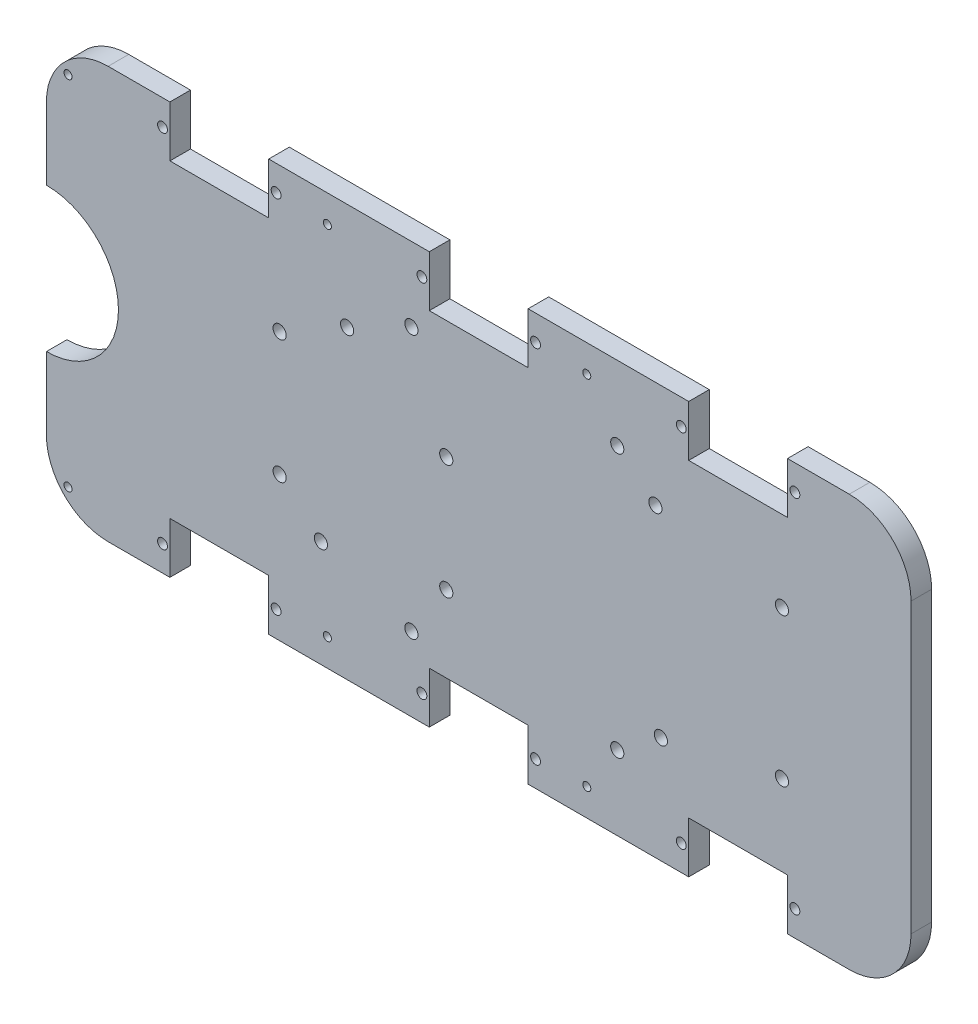
SolidWorks part; units mm, degrees
ref_plane "Front Plane" through (0, 0, 0) normal (0, 0, 1) x (1, 0, 0)
ref_plane "Top Plane" through (0, 0, 0) normal (0, 1, 0) x (1, 0, 0)
ref_plane "Right Plane" through (0, 0, 0) normal (1, 0, 0) x (0, 0, -1)
sketch "Sketch1" plane through (0, 0, 0) normal (0, 0, 1) x (1, 0, 0)
  line L1 (-90, -50) -> (90, -50)
  line L2 (-105, -35) -> (-105, 35)
  line L3 (-90, 50) -> (90, 50)
  line L4 (105, -35) -> (105, 35)
  line L5 (-105, -50) -> (105, 50) construction
  line L6 (-105, 50) -> (105, -50) construction
  arc A0 (-105, -35) -> (-90, -50) centre (-90, -35) ccw
  arc A1 (90, -50) -> (105, -35) centre (90, -35) ccw
  arc A2 (105, 35) -> (90, 50) centre (90, 35) ccw
  arc A3 (-90, 50) -> (-105, 35) centre (-90, 35) ccw
  point P0 (0, 0)
  dimension "D3" = 15
  dimension "D1" = 210
  dimension "D2" = 100
extrude "Boss-Extrude2" add sketch "Sketch1" along normal blind 5
sketch "Sketch2" plane through (0, 0, 5) normal (0, 0, 1) x (1, 0, 0)
  line L0 (-105, 0) -> (-75, 0) construction
  line L1 (-105, 35) -> (-105, -35) construction
  line L2 (-75, 0) -> (-51, 0) construction
  line L3 (-51, 0) -> (-12, 0) construction
  line L4 (-12, 0) -> (12, 0) construction
  line L5 (12, 0) -> (51, 0) construction
  line L6 (51, 0) -> (75, 0) construction
  line L7 (-75, 0) -> (-75, 50) construction
  line L8 (90, 50) -> (-90, 50) construction
  line L9 (-51, 0) -> (-51, 50) construction
  line L10 (-12, 0) -> (-12, 50) construction
  line L11 (12, 0) -> (12, 50) construction
  line L12 (51, 0) -> (51, 50) construction
  line L13 (75, 0) -> (75, 50) construction
  line L14 (-75, 0) -> (-75, -50) construction
  line L15 (-90, -50) -> (90, -50) construction
  line L16 (-51, 0) -> (-51, -50) construction
  line L17 (-12, 0) -> (-12, -50) construction
  line L18 (12, 0) -> (12, -50) construction
  line L19 (51, 0) -> (51, -50) construction
  line L20 (75, 0) -> (75, -50) construction
  line L21 (51, -37.6) -> (75, -37.6)
  line L22 (-75, 50) -> (-51, 50)
  line L23 (-75, 50) -> (-75, 37.6)
  line L24 (-75, 37.6) -> (-51, 37.6)
  line L25 (-51, 50) -> (-51, 37.6)
  line L26 (-12, 50) -> (12, 50)
  line L27 (-12, 50) -> (-12, 37.6)
  line L28 (-12, 37.6) -> (12, 37.6)
  line L29 (12, 50) -> (12, 37.6)
  line L30 (51, 50) -> (75, 50)
  line L31 (51, 50) -> (51, 37.6)
  line L32 (51, 37.6) -> (75, 37.6)
  line L33 (75, 50) -> (75, 37.6)
  line L34 (75, -50) -> (75, -37.6)
  line L35 (51, -50) -> (75, -50)
  line L36 (51, -50) -> (51, -37.6)
  line L37 (-12, -37.6) -> (12, -37.6)
  line L38 (12, -50) -> (12, -37.6)
  line L39 (-12, -50) -> (12, -50)
  line L40 (-12, -50) -> (-12, -37.6)
  line L41 (-75, -37.6) -> (-51, -37.6)
  line L42 (-51, -50) -> (-51, -37.6)
  line L43 (-75, -50) -> (-51, -50)
  line L44 (-75, -50) -> (-75, -37.6)
  dimension "D1" = 30
  dimension "D2" = 24
  dimension "D3" = 39
  dimension "D4" = 24
  dimension "D5" = 39
  dimension "D6" = 24
  dimension "D7" = 12.4
  dimension "D8" = 12.4
extrude "Cut-Extrude1" cut sketch "Sketch2" against normal blind 5
sketch "Sketch3" plane through (0, 0, 5) normal (0, 0, 1) x (1, 0, 0)
  line L0 (-51, 50) -> (-51, 37.6) construction
  line L1 (-105, 0) -> (105, 0) construction
  line L2 (-75, 50) -> (-75, 37.6) construction
  line L3 (-105, 35) -> (-105, -35) construction
  line L4 (-75, 43.8) -> (-76.8, 43.8) construction
  line L5 (-51, 43.8) -> (-49.2, 43.8) construction
  line L6 (105, -35) -> (105, 35) construction
  circle A0 centre (-76.8, 43.8) radius 1.2
  circle A1 centre (-49.2, 43.8) radius 1.2
  circle A2 centre (-13.8, 43.8) radius 1.2
  circle A3 centre (13.8, 43.8) radius 1.2
  circle A4 centre (49.2, 43.8) radius 1.2
  circle A5 centre (76.8, 43.8) radius 1.2
  circle A6 centre (-76.8, -43.8) radius 1.2
  circle A7 centre (-49.2, -43.8) radius 1.2
  circle A8 centre (-13.8, -43.8) radius 1.2
  circle A9 centre (13.8, -43.8) radius 1.2
  circle A10 centre (49.2, -43.8) radius 1.2
  circle A11 centre (76.8, -43.8) radius 1.2
  dimension "D2" = 1.8
  dimension "D3" = 3
  dimension "D1" = 1.8
extrude "Cut-Extrude2" cut sketch "Sketch3" against normal blind 5
sketch "Sketch5" plane through (0, 0, 5) normal (0, 0, 1) x (1, 0, 0)
  line L0 (-51, 50) -> (-51, 37.6) construction
  line L1 (105, 0) -> (-95.1885, 0) construction
  line L2 (-12, 50) -> (-51, 50) construction
  line L3 (-51, 37.6) -> (-51, 50) construction
  line L4 (-31.5, 50) -> (-36.75, 50) construction
  line L5 (-36.75, 50) -> (-36.75, 43.3602) construction
  circle A4 centre (-36.75, 43.3602) radius 0.975
  circle A5 centre (26.25, 43.3602) radius 0.975
  circle A6 centre (26.25, -43.3602) radius 0.975
  circle A7 centre (-36.75, -43.3602) radius 0.975
  circle A8 centre (-99.75, 43.3602) radius 0.975
  circle A9 centre (-99.75, -43.3602) radius 0.975
  point P13 (105, 0)
  dimension "D1" = 2
  dimension "D2" = 2
extrude "Cut-Extrude3" cut sketch "Sketch5" against normal blind 10
sketch "Sketch6" plane through (0, 0, 5) normal (0, 0, 1) x (1, 0, 0)
  line L0 (75, 37.6) -> (75, -37.6) construction
  line L1 (-105, 35) -> (-105, -35) construction
  circle A0 centre (-105, 0) radius 17.5
extrude "Cut-Extrude4" cut sketch "Sketch6" against normal blind 10
sketch "Sketch8" plane through (0, 0, 0) normal (0, 0, -1) x (-1, 0, 0)
  line L0 (-63, 37.6) -> (-63, 0) construction
  line L1 (-51, 37.6) -> (-75, 37.6) construction
  line L2 (-63, 0) -> (-8.65, 0) construction
  line L3 (-8.65, 0) -> (31.97, 0) construction
  line L4 (31.97, 0) -> (31.97, 24.11) construction
  line L5 (-8.65, 0) -> (-8.65, -24.11) construction
  line L6 (-8.65, 0) -> (-42.91, 0) construction
  line L7 (-8.65, -24.11) -> (38.33, -24.11) construction
  line L8 (-8.65, 0) -> (7.88, 0) construction
  line L9 (7.88, 0) -> (7.88, -19.03) construction
  line L10 (7.88, 0) -> (7.88, 8.88) construction
  line L11 (-42.91, 0) -> (-42.91, 24.11) construction
  line L12 (-8.65, -24.11) -> (-44.24, -24.11) construction
  line L13 (-8.65, 0) -> (48.35, 0) construction
  line L14 (48.35, 0) -> (48.35, 15) construction
  line L15 (-8.65, 0) -> (-73.65, 0) construction
  line L16 (-73.65, 0) -> (-73.65, 18) construction
  line L17 (-8.65, 0) -> (-8.65, 32) construction
  line L18 (-8.65, 32) -> (-33.65, 32) construction
  circle A0 centre (31.97, 24.11) radius 1.6
  circle A3 centre (38.33, -24.11) radius 1.6
  circle A4 centre (7.88, 8.88) radius 1.6
  circle A5 centre (7.88, -19.03) radius 1.6
  circle A6 centre (-42.91, 24.11) radius 1.6
  circle A8 centre (-44.24, -24.11) radius 1.6
  circle A9 centre (-73.65, 18) radius 1.6
  circle A10 centre (48.35, 15) radius 1.6
  circle A11 centre (-73.65, -18) radius 1.6
  circle A12 centre (48.35, -15) radius 1.6
  circle A13 centre (-33.65, 32) radius 1.6
  circle A14 centre (16.35, 32) radius 1.6
  circle A15 centre (-33.65, -32) radius 1.6
  circle A16 centre (16.35, -32) radius 1.6
  dimension "D4" = 46.98
  dimension "D5" = 16.53
  dimension "D8" = 34.26
  dimension "D9" = 24.11
  dimension "D11" = 57
  dimension "D15" = 32
  dimension "D1" = 54.35
  dimension "D2" = 40.62
  dimension "D3" = 24.11
  dimension "D6" = 19.03
  dimension "D7" = 8.88
  dimension "D10" = 35.59
  dimension "D12" = 15
  dimension "D13" = 65
  dimension "D14" = 18
  dimension "D16" = 25
extrude "Cut-Extrude5" cut sketch "Sketch8" against normal blind 10
sketch "Sketch10" plane through (0, 0, 0) normal (0, 0, -1) x (-1, 0, 0)
  line L0 (71.2901, 0) -> (71.2901, -11.5)
  line L2 (76.2901, 0) -> (76.2901, -16.5)
  line L3 (65.0901, 11.5) -> (65.0901, 0) construction
  line L13 (53.8901, -16.5) -> (76.2901, -16.5)
  line L14 (53.8901, 16.5) -> (53.8901, -16.5)
  line L15 (87.5, 0) -> (71.2901, 0) construction
  line L16 (58.8901, 11.5) -> (71.2901, 11.5)
  line L17 (58.8901, 11.5) -> (58.8901, -11.5)
  line L18 (58.8901, -11.5) -> (71.2901, -11.5)
  line L20 (58.8901, 11.5) -> (71.2901, -11.5) construction
  line L21 (58.8901, -11.5) -> (71.2901, 11.5) construction
  line L24 (53.8901, 16.5) -> (71.2901, 16.5)
  line L25 (71.2901, 11.5) -> (71.2901, 16.5)
  line L26 (71.2901, 0) -> (76.2901, 0)
  line L27 (53.8901, 16.5) -> (76.2901, 16.5) construction
  line L28 (76.2901, 16.5) -> (76.2901, -16.5) construction
  line L29 (71.2901, 11.5) -> (71.2901, -11.5) construction
  arc A0 (105, 17.5) -> (105, -17.5) centre (105, 0) ccw construction
  dimension "D1" = 22.4099
  dimension "D2" = 23
  dimension "D3" = 12.4
  dimension "D4" = 5
extrude "Boss-Extrude3" add sketch "Sketch10" along normal blind 17.7
sketch "Sketch12" plane through (0, 0, -17.7) normal (0, 0, -1) x (-1, 0, 0)
  line L0 (58.8901, 0) -> (96.2, 0) construction
  line L1 (58.8901, 11.5) -> (58.8901, -11.5) construction
  line L3 (65.0901, 34.0148) -> (65.0901, -11.5) construction
  line L4 (58.8901, -11.5) -> (71.2901, -11.5) construction
  line L5 (65.0901, -11.5) -> (65.0901, -13.8) construction
  line L6 (58.8901, 0) -> (71.2901, 0) construction
  circle A0 centre (65.0901, -13.8) radius 1.2
  circle A1 centre (65.0901, 13.8) radius 1.2
  dimension "D1" = 2.3
extrude "Cut-Extrude6" cut sketch "Sketch12" against normal blind 5
